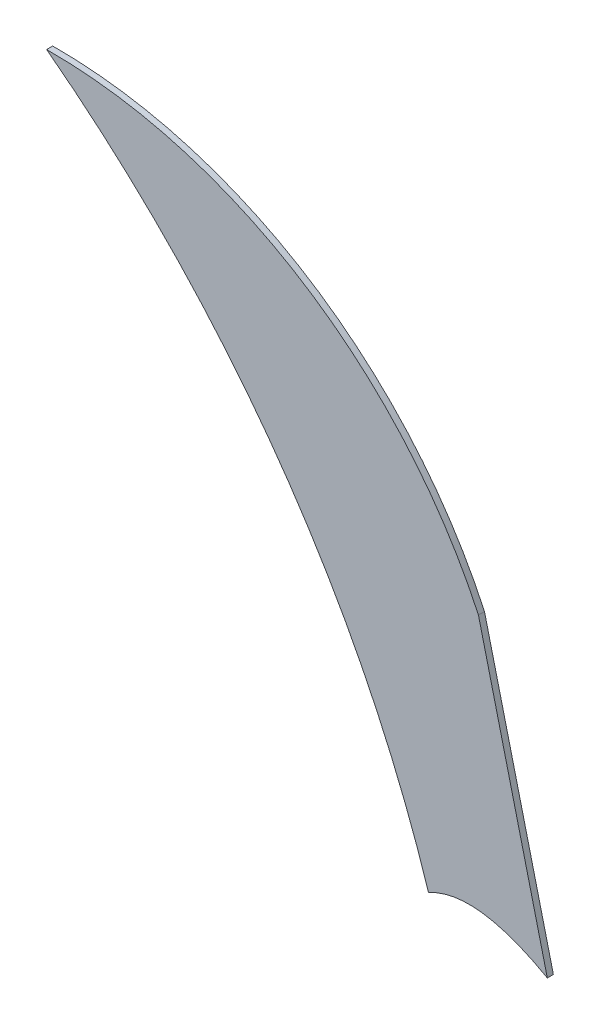
SolidWorks part; units mm, degrees
ref_plane "Alzado" through (0, 0, 0) normal (0, 0, 1) x (1, 0, 0)
ref_plane "Planta" through (0, 0, 0) normal (0, 1, 0) x (1, 0, 0)
ref_plane "Vista lateral" through (0, 0, 0) normal (1, 0, 0) x (0, 0, -1)
sketch "Model" plane through (0, 0, 0) normal (0, 0, 1) x (1, 0, 0)
  arc A0 (37.9114, 21.3069) -> (30.7774, 25.8308) centre (30.8244, 18.0179) ccw
  arc A1 (37.0863, 16.9236) -> (30.7774, 25.8308) centre (19.8862, 11.4287) ccw
  spline S0 degree 2 poles (39.0499, 16.6826) (37.8662, 17.352) (37.0863, 16.9236) knots 1 1 1 1.517629 1.517629 1.517629
  spline S1 degree 2 poles (37.9114, 21.3069) (38.4806, 18.9947) (39.0499, 16.6826) knots 0 0 0 1 1 1
extrude "Saliente-Extruir1" add sketch "Model" along normal blind 0.1
